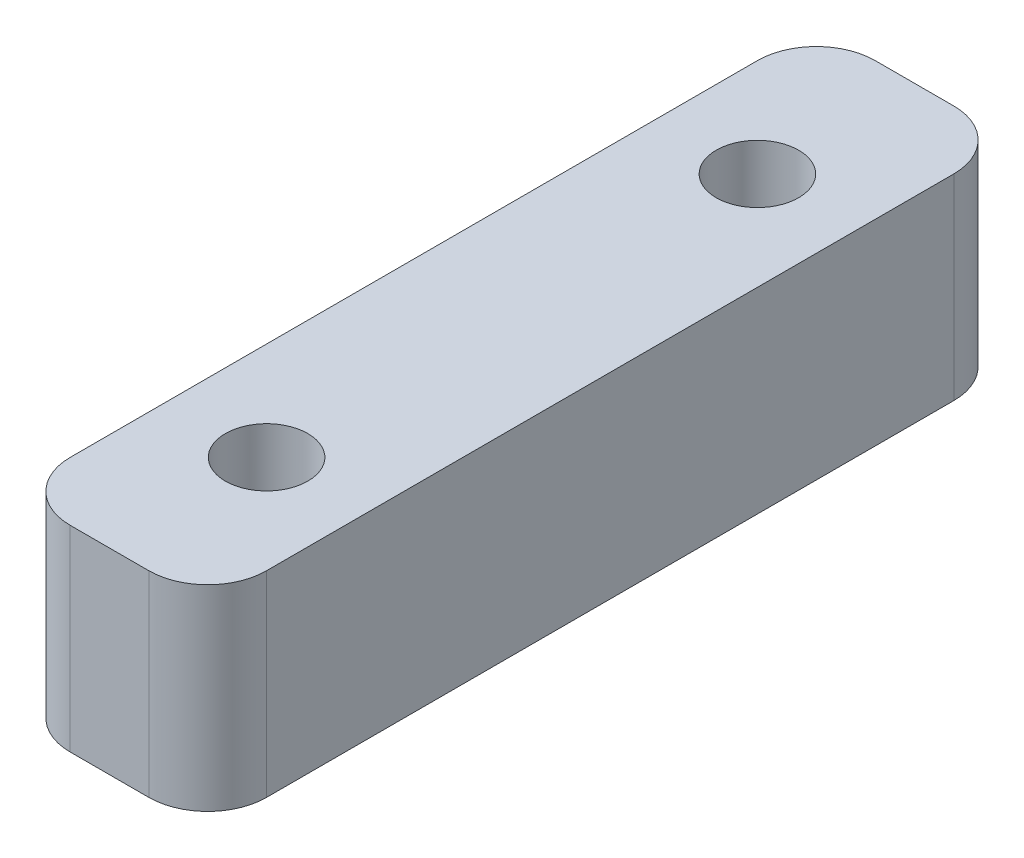
SolidWorks part; units mm, degrees
material "Thornel Mat VMA"
ref_plane "前视基准面" through (0, 0, 0) normal (0, 0, 1) x (1, 0, 0)
ref_plane "上视基准面" through (0, 0, 0) normal (0, 1, 0) x (1, 0, 0)
ref_plane "右视基准面" through (0, 0, 0) normal (1, 0, 0) x (0, 0, -1)
sketch "草图1" plane through (0, 0, 0) normal (0, 1, 0) x (1, 0, 0)
  line L1 (-12.5, 10) -> (12.5, 10) construction
  line L2 (-12.5, 10) -> (-12.5, -10) construction
  line L3 (-12.5, -10) -> (12.5, -10) construction
  line L4 (12.5, 10) -> (12.5, -10) construction
  line L5 (0, -10) -> (0, 10) construction
  line L6 (-12.5, 0) -> (12.5, 0) construction
  line L7 (-27.5, 16) -> (27.5, 16)
  line L8 (-27.5, 16) -> (-27.5, -16)
  line L9 (-27.5, -16) -> (27.5, -16)
  line L10 (27.5, 16) -> (27.5, -16)
  line L11 (0, -16) -> (0, 16) construction
  line L12 (-27.5, 0) -> (27.5, 0) construction
  circle A0 centre (-12.5, 10) radius 2.1
  circle A1 centre (12.5, 10) radius 2.1
  circle A2 centre (12.5, -10) radius 2.1
  circle A3 centre (-12.5, -10) radius 2.1
  point P0 (0, 0)
  point P8 (0, 0)
  dimension "D3" = 4.2
  dimension "D1" = 20
  dimension "D2" = 25
  dimension "D4" = 6
  dimension "D5" = 55
extrude "凸台-拉伸1" add sketch "草图1" along normal blind 10
sketch "草图2" plane through (0, 10, 0) normal (0, 1, 0) x (1, 0, 0)
  line L0 (-27.5, -16) -> (27.5, -16)
  line L1 (-27.5, -16) -> (-27.5, -20)
  line L2 (27.5, -16) -> (27.5, -20)
  line L3 (-27.5, -20) -> (27.5, -20)
  line L4 (27.5, -18) -> (-27.5, -18) construction
  line L5 (0, -16) -> (0, -20) construction
  point P154 (0, -18)
  dimension "D1" = 4
extrude "凸台-拉伸2" add sketch "草图2" against normal up to surface (10 mm away) up to face at (0, 0, 0)
sketch "草图4" plane through (0, 10, 0) normal (0, 1, 0) x (1, 0, 0)
  line L0 (0, -20) -> (0, -49669.0422) construction
  line L1 (-27.5, -20) -> (27.5, -20) construction
  line L2 (-12.5, -10) -> (12.5, -10) construction
  line L3 (-47.5, -65) -> (47.5, -65) construction
  line L4 (-47.5, -65) -> (-47.5, -90) construction
  line L5 (-47.5, -90) -> (47.5, -90) construction
  line L6 (47.5, -65) -> (47.5, -90) construction
  line L7 (0, -90) -> (0, -65) construction
  line L8 (-47.5, -77.5) -> (47.5, -77.5) construction
  line L9 (-27.5, -20) -> (-27.5, -57)
  line L10 (-27.5, -20) -> (27.5, -20)
  line L11 (-67.5, -57) -> (-27.5, -57)
  line L12 (-67.5, -57) -> (-67.5, -98)
  line L13 (-67.5, -98) -> (67.5, -98)
  line L14 (67.5, -57) -> (67.5, -98)
  line L15 (0, -98) -> (0, -20) construction
  line L16 (-67.5, -77.5) -> (67.5, -77.5) construction
  line L17 (27.5, -20) -> (27.5, -57)
  line L18 (27.5, -57) -> (67.5, -57)
  line L19 (-62, -57) -> (-62, -98) construction
  circle A0 centre (-47.5, -65) radius 2.1
  circle A1 centre (-47.5, -90) radius 2.1
  circle A2 centre (47.5, -90) radius 2.1
  circle A3 centre (47.5, -65) radius 2.1
  circle A4 centre (-62, -88) radius 1.6
  circle A5 centre (-62, -80) radius 1.6
  circle A6 centre (62, -88) radius 1.6
  circle A7 centre (62, -80) radius 1.6
  point P4 (0, -20)
  point P5 (0, -77.5)
  point P16 (0, -77.5)
  dimension "D4" = 4.2
  dimension "D8" = 3.2
  dimension "D1" = 25
  dimension "D2" = 95
  dimension "D3" = 55
  dimension "D5" = 8
  dimension "D6" = 20
  dimension "D7" = 14.5
  dimension "D9" = 8
  dimension "D10" = 2
extrude "凸台-拉伸3" add sketch "草图4" against normal up to surface (10 mm away) up to face at (0, 0, 2)
sketch "草图6" plane through (0, 10, 0) normal (0, 1, 0) x (1, 0, 0)
  line L0 (0, 16) -> (0, -49984) construction
  line L1 (-115, -127.5) -> (-95, -127.5) construction
  line L2 (-115, -127.5) -> (-115, -137.5) construction
  line L3 (-115, -137.5) -> (-95, -137.5) construction
  line L4 (-95, -127.5) -> (-95, -137.5) construction
  line L5 (-105, -137.5) -> (-105, -127.5) construction
  line L6 (-115, -132.5) -> (-95, -132.5) construction
  line L7 (27.5, 16) -> (-27.5, 16) construction
  line L8 (-121, -122.5) -> (-105, -122.5)
  line L9 (-121, -122.5) -> (-121, -142.5)
  line L10 (-121, -142.5) -> (-89, -142.5)
  line L12 (-105, -142.5) -> (-105, -122.5) construction
  line L13 (-121, -132.5) -> (-89, -132.5) construction
  line L14 (-70.5, -108) -> (-70.5, -98) construction
  line L15 (-70.5, -108) -> (70.5, -108) construction
  line L16 (-70.5, -98) -> (70.5, -98) construction
  line L17 (70.5, -108) -> (70.5, -98) construction
  line L18 (-70.5, -108) -> (70.5, -98) construction
  line L19 (-70.5, -98) -> (70.5, -108) construction
  line L20 (-67.5, -98) -> (67.5, -98) construction
  line L21 (-67.5, -98) -> (-89, -142.5)
  line L22 (-105, -122.5) -> (-83.2155, -68)
  line L24 (-67.5, -68) -> (-67.5, -98)
  line L26 (-67.5, -68) -> (-83.2155, -68)
  line L27 (47.5, -68) -> (67.5, -68) construction
  line L28 (70.5, -108) -> (70.5, -98) construction
  line L29 (121, -132.5) -> (89, -132.5) construction
  line L30 (105, -142.5) -> (105, -122.5) construction
  line L31 (115, -132.5) -> (95, -132.5) construction
  line L32 (105, -137.5) -> (105, -127.5) construction
  line L33 (95, -127.5) -> (95, -137.5) construction
  line L34 (115, -137.5) -> (95, -137.5) construction
  line L35 (115, -127.5) -> (115, -137.5) construction
  line L36 (115, -127.5) -> (95, -127.5) construction
  line L37 (67.5, -68) -> (83.2155, -68)
  line L38 (67.5, -68) -> (67.5, -98)
  line L39 (105, -122.5) -> (83.2155, -68)
  line L40 (67.5, -98) -> (89, -142.5)
  line L41 (121, -142.5) -> (89, -142.5)
  line L42 (121, -122.5) -> (121, -142.5)
  line L43 (121, -122.5) -> (105, -122.5)
  circle A0 centre (-115, -127.5) radius 2.1
  circle A1 centre (-95, -127.5) radius 2.1
  circle A2 centre (-95, -137.5) radius 2.1
  circle A3 centre (-115, -137.5) radius 2.1
  circle A4 centre (-47.5, -90) radius 2.1 construction
  circle A5 centre (-47.5, -90) radius 2.1 construction
  circle A6 centre (115, -137.5) radius 2.1
  circle A7 centre (95, -137.5) radius 2.1
  circle A8 centre (95, -127.5) radius 2.1
  circle A9 centre (115, -127.5) radius 2.1
  point P0 (-105, -132.5)
  point P12 (-105, -132.5)
  point P19 (0, 16)
  point P21 (0, -103)
  point P54 (105, -132.5)
  dimension "D3" = 4.2
  dimension "D1" = 20
  dimension "D2" = 10
  dimension "D4" = 47.5
  dimension "D5" = 37.5
  dimension "D6" = 20
  dimension "D7" = 6
  dimension "D8" = 141
  dimension "D9" = 10
  dimension "D10" = 4
  dimension "D11" = 30
extrude "凸台-拉伸4" add sketch "草图6" against normal up to surface (10 mm away) up to face at (0, 0, 49)
sketch "草图7" plane through (0, 10, 0) normal (0, 1, 0) x (1, 0, 0)
  line L0 (0, 16) -> (0, -49984) construction
  line L1 (27.5, 16) -> (-27.5, 16) construction
  line L2 (-67.5, -57) -> (-67.5, -68)
  line L3 (-67.5, -57) -> (-52.5, -57)
  line L4 (-67.5, -68) -> (-52.5, -68)
  line L5 (-52.5, -57) -> (-52.5, -68)
  line L6 (-60, -68) -> (-60, -57) construction
  line L7 (-67.5, -62.5) -> (-52.5, -62.5) construction
  line L8 (67.5, -68) -> (52.5, -68)
  line L9 (52.5, -57) -> (52.5, -68)
  line L10 (67.5, -57) -> (52.5, -57)
  line L11 (67.5, -57) -> (67.5, -68)
  point P4 (0, 16)
  point P147 (-60, -62.5)
  dimension "D1" = 15
extrude "切除-拉伸1" cut sketch "草图7" against normal through all
sketch "草图8" plane through (0, 10, 0) normal (0, 1, 0) x (1, 0, 0)
  line L0 (-12.5, -10) -> (12.5, -10) construction
  line L1 (-27.5, -20) -> (27.5, -20) construction
  line L2 (-27.5, 16) -> (-27.5, -57) construction
  line L3 (27.5, -57) -> (27.5, 16) construction
  line L4 (-27.5, -20) -> (-39.5, -57)
  line L5 (-27.5, -57) -> (-52.5, -57) construction
  line L6 (-39.5, -57) -> (-27.5, -57)
  line L7 (-27.5, -57) -> (-27.5, -20)
  line L8 (0, 16) -> (0, -49984) construction
  line L9 (27.5, 16) -> (-27.5, 16) construction
  line L10 (-47.5, -65) -> (-47.5, -90) construction
  line L11 (39.5, -57) -> (27.5, -57)
  line L12 (27.5, -20) -> (39.5, -57)
  line L13 (27.5, -57) -> (27.5, -20)
  point P19 (0, 16)
  point P20 (0, -10)
  dimension "D1" = 10
  dimension "D2" = 8
extrude "凸台-拉伸5" add sketch "草图8" against normal up to surface (10 mm away) up to face at (0, 0, 86.2)
sketch "草图9" plane through (0, 10, 0) normal (0, 1, 0) x (1, 0, 0)
  line L0 (-52.5, -68) -> (-52.5, -57) construction
  line L1 (-39.5, -57) -> (-52.5, -57) construction
  line L2 (0, 16) -> (0, -49984) construction
  line L3 (27.5, 16) -> (-27.5, 16) construction
  circle A1 centre (-30, -67) radius 1.5
  circle A3 centre (-15, -67) radius 1.5
  circle A4 centre (15, -67) radius 1.5
  circle A5 centre (30, -67) radius 1.5
  point P13 (0, 16)
  dimension "D4" = 3
  dimension "D1" = 15
  dimension "D2" = 22.5
  dimension "D3" = 10
extrude "切除-拉伸2" cut sketch "草图9" against normal through all
fillet "圆角1" [suppressed] radius 3
sketch "草图10" plane through (0, 10, 0) normal (0, 1, 0) x (1, 0, 0)
  line L0 (0, 16) -> (0, -49984) construction
  line L1 (27.5, 16) -> (-27.5, 16) construction
  line L2 (-47.5, -65) -> (-47.5, -90) construction
  line L3 (-52.5, -68) -> (-52.5, -57) construction
  line L4 (-42.5, -98) -> (-52.5, -98)
  line L5 (-42.5, -98) -> (-42.5, -57)
  line L6 (-42.5, -57) -> (-52.5, -57)
  line L7 (-52.5, -98) -> (-52.5, -57)
  line L8 (-47.5, -57) -> (-47.5, -98) construction
  line L9 (-42.5, -77.5) -> (-52.5, -77.5) construction
  line L10 (-39.5, -57) -> (-52.5, -57) construction
  point P4 (0, 16)
  point P9 (-47.5, -77.5)
extrude "切除-拉伸3" cut sketch "草图10" against normal through all flip side to cut
fillet "圆角2" radius 3 4 edges at (-42.5, 5, 98) (-42.5, 5, 57) (-52.5, 5, 57) (-52.5, 5, 98)
